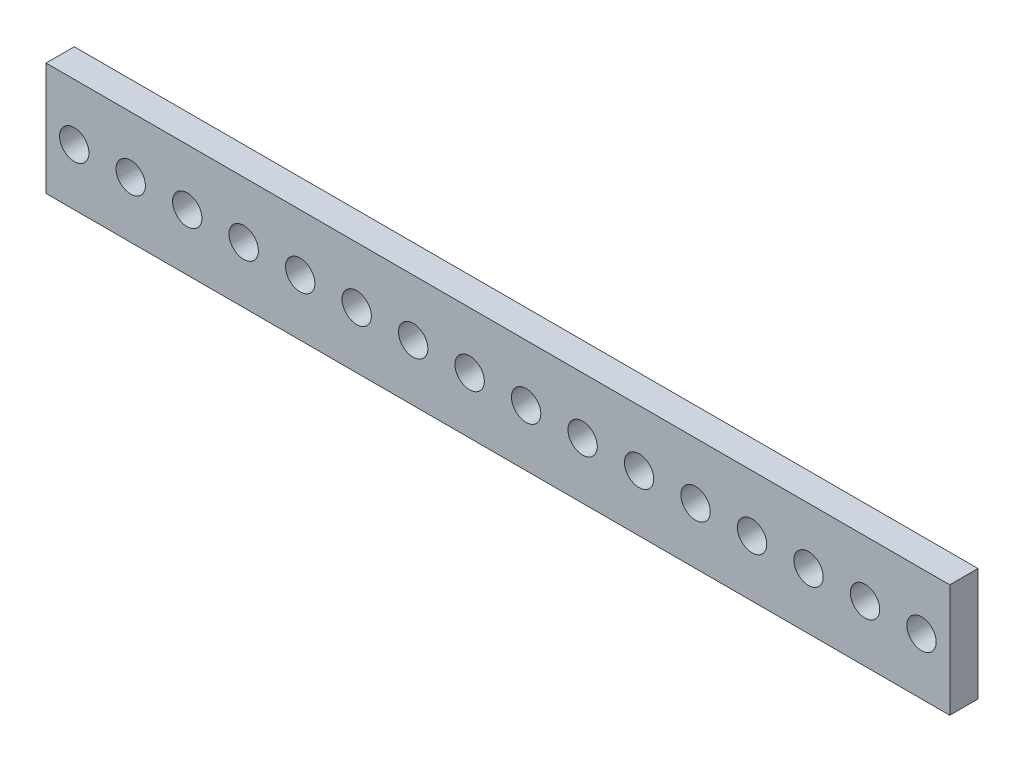
SolidWorks part; units mm, degrees
ref_plane "Front Plane" through (0, 0, 0) normal (0, 0, 1) x (1, 0, 0)
ref_plane "Top Plane" through (0, 0, 0) normal (0, 1, 0) x (1, 0, 0)
ref_plane "Right Plane" through (0, 0, 0) normal (1, 0, 0) x (0, 0, -1)
sketch "Sketch1" plane through (0, 0, 0) normal (0, 0, 1) x (1, 0, 0)
  line L1 (0, 0) -> (101.6, 0)
  line L2 (0, 0) -> (0, 12.7)
  line L3 (0, 12.7) -> (101.6, 12.7)
  line L4 (101.6, 0) -> (101.6, 12.7)
  dimension "D1" = 12.7
  dimension "D2" = 101.6
extrude "Boss-Extrude3" add sketch "Sketch1" along normal blind 3.175
sketch "Sketch2" plane through (0, 0, 0) normal (0, 0, 1) x (1, 0, 0)
  line L0 (0, 6.35) -> (101.6, 6.35) construction
  line L1 (0, 12.7) -> (0, 0) construction
  line L2 (101.6, 0) -> (101.6, 12.7) construction
  line L3 (50.8, 12.7) -> (50.8, 0) construction
  line L4 (101.6, 12.7) -> (0, 12.7) construction
  line L5 (0, 0) -> (101.6, 0) construction
  circle A0 centre (3.175, 6.35) radius 1.651
  circle A1 centre (9.525, 6.35) radius 1.651
  circle A2 centre (15.875, 6.35) radius 1.651
  circle A3 centre (22.225, 6.35) radius 1.651
  circle A4 centre (28.575, 6.35) radius 1.651
  circle A5 centre (34.925, 6.35) radius 1.651
  circle A6 centre (41.275, 6.35) radius 1.651
  circle A7 centre (47.625, 6.35) radius 1.651
  circle A8 centre (53.975, 6.35) radius 1.651
  circle A9 centre (60.325, 6.35) radius 1.651
  circle A10 centre (66.675, 6.35) radius 1.651
  circle A11 centre (73.025, 6.35) radius 1.651
  circle A12 centre (79.375, 6.35) radius 1.651
  circle A13 centre (85.725, 6.35) radius 1.651
  circle A14 centre (92.075, 6.35) radius 1.651
  circle A15 centre (98.425, 6.35) radius 1.651
  point P58 (-2.2111, 15.7133)
  dimension "D16" = 3.302
  dimension "D8" = 3.175
  dimension "D9" = 6.35
  dimension "D10" = 6.35
  dimension "D11" = 6.35
  dimension "D12" = 6.35
  dimension "D13" = 6.35
  dimension "D14" = 6.35
  dimension "D15" = 6.35
extrude "Cut-Extrude1" cut sketch "Sketch2" against normal blind 127 and the other way blind 127 contours A0 | A1 | A2 | A3 | A4 | A5 | A6 | A7 | A8 | A9 | A10 | A11 | A12 | A13 | A14 | A15
